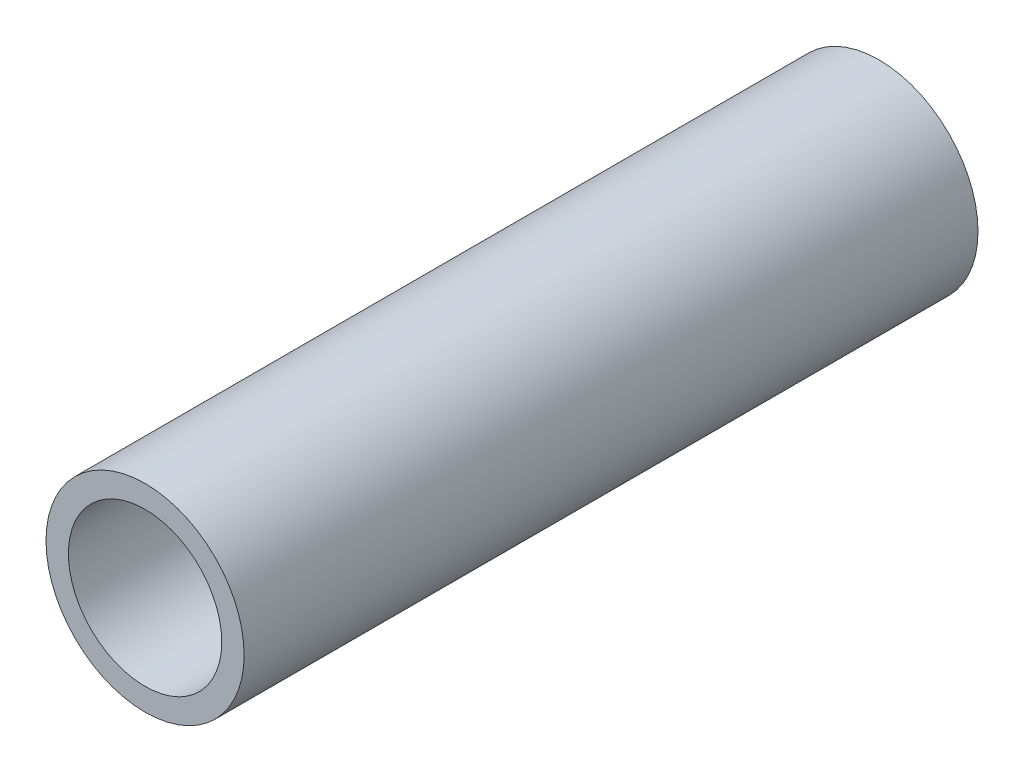
SolidWorks part; units mm, degrees
ref_plane "Front Plane" through (0, 0, 0) normal (0, 0, 1) x (1, 0, 0)
ref_plane "Top Plane" through (0, 0, 0) normal (0, 1, 0) x (1, 0, 0)
ref_plane "Right Plane" through (0, 0, 0) normal (1, 0, 0) x (0, 0, -1)
sketch "Sketch1" plane through (0, 0, 0) normal (0, 0, 1) x (1, 0, 0)
  circle A0 centre (0, 0) radius 4.18
  circle A1 centre (0, 0) radius 5.4
extrude "Boss-Extrude1" add sketch "Sketch1" along normal blind 40
sketch "Sketch2" plane through (0, 0, 0) normal (1, 0, 0) x (0, 0, -1)
  circle A0 centre (-20, 0) radius 3
extrude "Cut-Extrude1" cut sketch "Sketch2" against normal up to next
